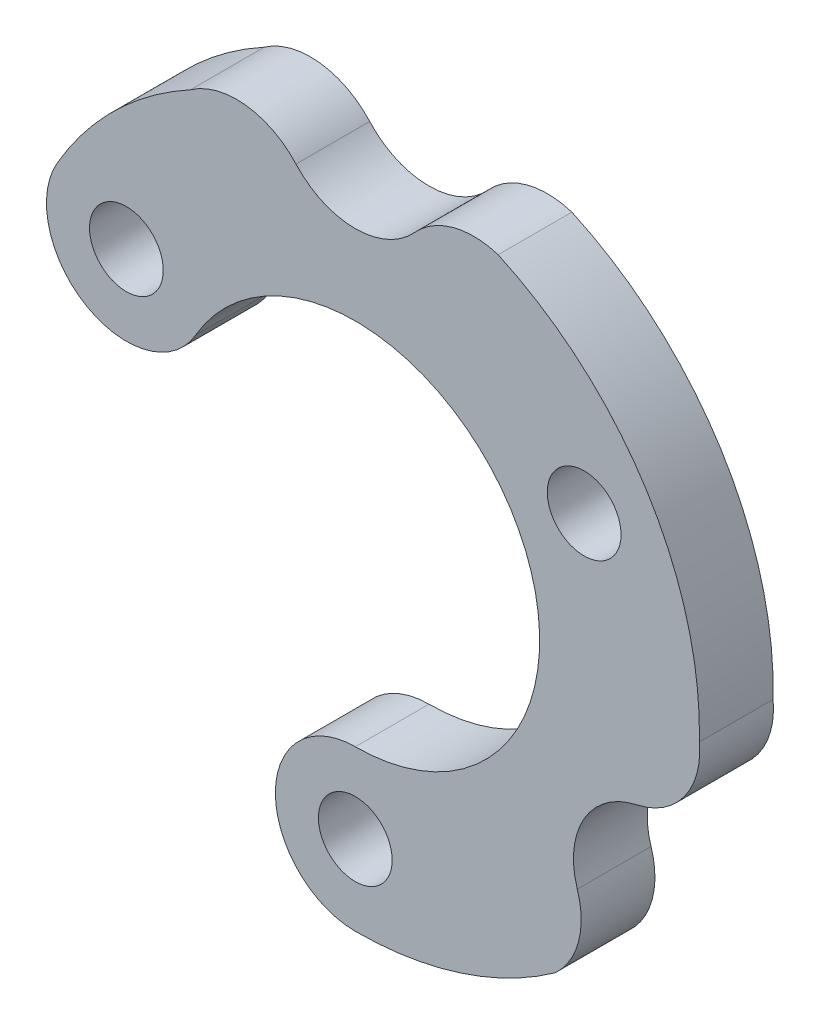
SolidWorks part; units mm, degrees
ref_plane "Plan de face" through (0, 0, 0) normal (0, 0, 1) x (1, 0, 0)
ref_plane "Plan de dessus" through (0, 0, 0) normal (0, 1, 0) x (1, 0, 0)
ref_plane "Plan de droite" through (0, 0, 0) normal (1, 0, 0) x (0, 0, -1)
sketch "Esquisse1" plane through (0, 0, 0) normal (0, 0, 1) x (1, 0, 0)
  line L0 (9.3098, 5.375) -> (0, -10.75) construction
  line L1 (0, -10.75) -> (-1.625, -7.9354) construction
  line L2 (-9.3098, 5.375) -> (9.3098, 5.375) construction
  line L3 (-7.2702, 1.8423) -> (-9.3098, 5.375) construction
  arc A12 (-2.411, 11.8207) -> (2.411, 11.8207) centre (0, 14) ccw
  arc A16 (5.8094, 12.7378) -> (2.411, 11.8207) centre (4.8221, 9.6414) ccw
  arc A17 (-2.411, 11.8207) -> (-6.7074, 12.2887) centre (-4.8221, 9.6414) ccw
  arc A18 (-6.7074, 12.2887) -> (-12.1244, 7) centre (0, 0) ccw
  arc A19 (8.1265, -11.4) -> (9.0315, -7.9984) centre (5.9386, -8.9967) ccw
  arc A20 (11.4425, -3.8223) -> (9.0315, -7.9984) centre (12.1244, -7) ccw
  arc A21 (11.4425, -3.8223) -> (13.996, -0.3356) centre (10.7607, -0.6447) ccw
  arc A27 (0, -14) -> (8.1265, -11.4) centre (0, 0) ccw
  arc A28 (13.996, -0.3356) -> (5.8094, 12.7378) centre (0, 0) ccw
  arc A30 (-3.2127, -10.2587) -> (-10.4906, 2.3471) centre (0, 0) ccw construction
  circle A31 centre (9.3098, 5.375) radius 1.5
  circle A32 centre (0, -10.75) radius 1.5
  circle A33 centre (-9.3098, 5.375) radius 1.5
  circle A34 centre (9.3098, 5.375) radius 3.25 construction
  arc A35 (-12.1244, 7) -> (-6.4952, 3.75) centre (-9.3098, 5.375) ccw
  arc A36 (0, -7.5) -> (0, -14) centre (0, -10.75) ccw
  arc A37 (0, -7.5) -> (-6.4952, 3.75) centre (0, 0) ccw
  arc A38 (-9.0315, -7.9984) -> (-7.2886, -11.9531) centre (-5.9386, -8.9967) ccw [skipped]
  arc A39 (-9.3098, -5.375) -> (-11.4425, -3.8223) centre (-12.1244, -7) ccw [skipped]
  arc A40 (-13.9359, -1.3378) -> (-11.4425, -3.8223) centre (-10.7607, -0.6447) ccw [skipped]
  point P31 (0, 0)
  dimension "D2" = 3
  dimension "D3" = 6.5
  dimension "D4" = 6.5
  dimension "D8" = 14
  dimension "D9" = 3.25
  dimension "D10" = 6.5
  dimension "D11" = 3.25
  dimension "D6" = 60
  dimension "D7" = 60
  dimension "D14" = 10.78
  dimension "D15" = 10.78
extrude "Boss.-Extru.2" add sketch "Esquisse1" along normal blind 3
